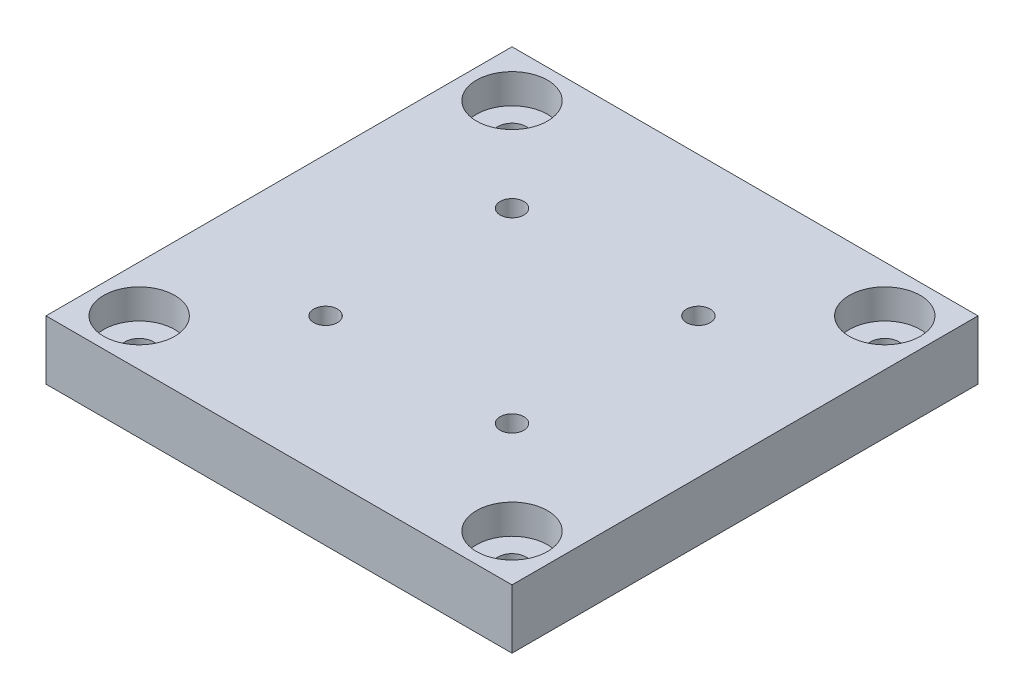
SolidWorks part; units mm, degrees
ref_plane "Front Plane" through (0, 0, 0) normal (0, 0, 1) x (1, 0, 0)
ref_plane "Top Plane" through (0, 0, 0) normal (0, 1, 0) x (1, 0, 0)
ref_plane "Right Plane" through (0, 0, 0) normal (1, 0, 0) x (0, 0, -1)
sketch "Sketch1" plane through (0, 0, 0) normal (0, 1, 0) x (1, 0, 0)
  line L0 (0, 0) -> (0, 49.9999)
  line L1 (0, 49.9999) -> (49.9999, 49.9999)
  line L2 (49.9999, 49.9999) -> (49.9999, 0)
  line L3 (49.9999, 0) -> (0, 0)
  circle A8 centre (4.9999, 45) radius 1.524
  circle A9 centre (45, 45) radius 1.524
  circle A10 centre (45, 4.9999) radius 1.524
  circle A11 centre (4.9999, 4.9999) radius 1.524
  circle A13 centre (14.9999, 35) radius 1.27
  circle A14 centre (35, 35) radius 1.27
  circle A15 centre (35, 14.9999) radius 1.27
  circle A16 centre (14.9999, 14.9999) radius 1.27
  point P8 (14.9283, 35.0716)
  point P13 (15.1864, 14.9999)
  point P15 (35.1909, 14.809)
extrude "Boss-Extrude1" add sketch "Sketch1" along normal blind 6.35
sketch "Sketch2" plane through (0, 6.35, 0) normal (0, 1, 0) x (1, 0, 0)
  circle A0 centre (4.9999, 45) radius 3.81
  circle A1 centre (45, 45) radius 3.81
  circle A2 centre (4.9999, 4.9999) radius 3.81
  circle A3 centre (45, 4.9999) radius 3.81
extrude "Cut-Extrude1" cut sketch "Sketch2" against normal blind 3.175
